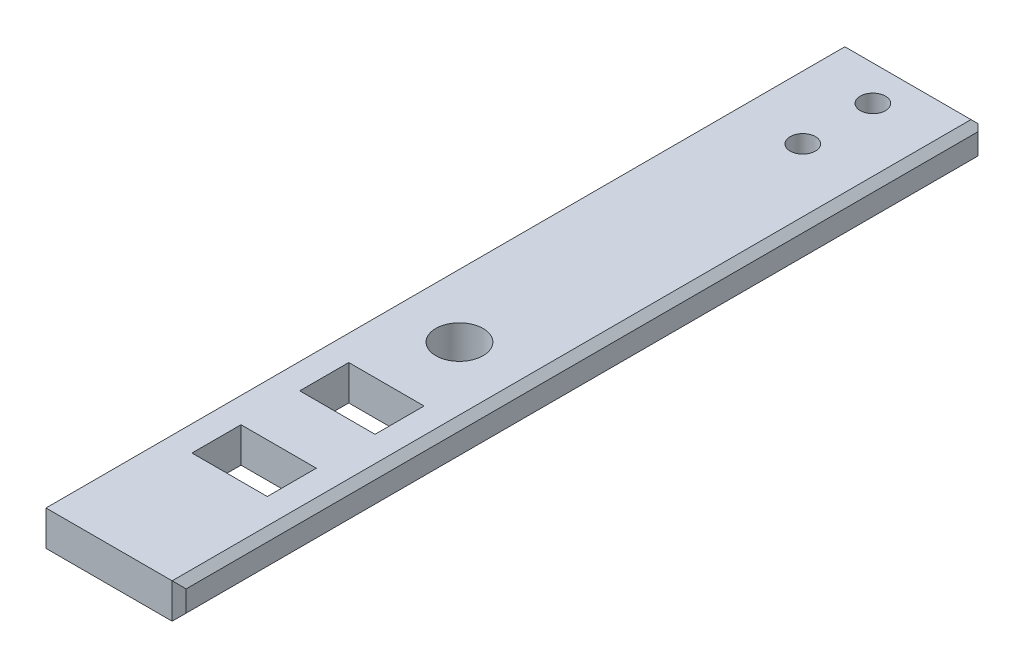
SolidWorks part; units mm, degrees
material "ABS"
ref_plane "Front Plane" through (0, 0, 0) normal (0, 0, 1) x (1, 0, 0)
ref_plane "Top Plane" through (0, 0, 0) normal (0, 1, 0) x (1, 0, 0)
ref_plane "Right Plane" through (0, 0, 0) normal (1, 0, 0) x (0, 0, -1)
sketch "Sketch1" plane through (0, 0, 0) normal (0, 1, 0) x (1, 0, 0)
  line L1 (0, 0) -> (20, 0)
  line L2 (0, 0) -> (0, 115)
  line L3 (0, 115) -> (20, 115)
  line L4 (20, 0) -> (20, 115)
  dimension "D1" = 20
  dimension "D2" = 115
extrude "Boss-Extrude1" add sketch "Sketch1" along normal blind 5
sketch "Sketch3" plane through (0, 0, 0) normal (0, -1, 0) x (1, 0, 0)
  line L1 (5, -25) -> (15, -25)
  line L2 (5, -25) -> (5, -33)
  line L3 (5, -33) -> (15, -33)
  line L4 (15, -25) -> (15, -33)
  line L5 (0, 0) -> (20, 0) construction
  line L6 (0, 0) -> (20, 0) construction
  point P4 (10, -25)
  point P5 (10, 0)
  dimension "D1" = 10
  dimension "D3" = 25
  dimension "D4" = 8
extrude "Boss-Extrude2" [suppressed] add sketch "Sketch3" along normal blind 12.5
sketch "Sketch13" [suppressed] plane through (10, 0, 0) normal (-1, 0, 0) x (0, 0, 1)
  line L4 (-25, 0) -> (-33, 0)
  line L5 (-33, 0) -> (-33, -12.5)
  line L6 (-33, -12.5) -> (-25, -12.5)
  line L7 (-25, -12.5) -> (-25, 0)
  line L8 (-25, 0) -> (-33, 0)
  line L9 (-33, 0) -> (-33, -12.5)
  line L10 (-33, -12.5) -> (-25, -12.5)
  line L11 (-25, -12.5) -> (-25, 0)
  dimension "D1" = 0
extrude "Cut-Extrude1" [suppressed] cut sketch "Sketch13" against normal mid plane 3.5
hole_wizard "M3 Clearance Hole5" [suppressed] positions "3DSketch5" profile "Sketch7" hole size "M3" standard "ANSI Metric"
sketch3d "3DSketch5" [suppressed]
  line L0 (5, -12.5, -25) -> (5, -12.5, -33) construction
  line L1 (5, -12.5, -33) -> (5, 0, -33) construction
  point P0 (5, -8.5, -29)
  dimension "D1" = 4
  dimension "D2" = 4
sketch "Sketch7" plane through (5, -8.5, -29) normal (0, 1, 0) x (0, 0, 1)
  line L0 (0, 0) -> (0, 15)
  line L1 (0, 15) -> (1.8, 15)
  line L2 (1.8, 15) -> (1.8, 0)
  line L5 (1.8, 0) -> (0, 0)
  line L11 (0, -6.35) -> (0, 107.95) construction
  dimension "Thru Hole Dia." = 3.6
  dimension "Thru Hole Depth" = 15
hole_wizard "E (0.29) Diameter Hole2" [suppressed] positions "3DSketch6" profile "Sketch8" hole size "E" standard "ANSI Inch"
sketch3d "3DSketch6"
  line L0 (20, 0, -75) -> (0, 0, -75) construction
  line L1 (20, 0, 0) -> (20, 0, -75) construction
  point P0 (10, 0, -40)
  dimension "D1" = 35
  dimension "D2" = 10
sketch "Sketch8" plane through (10, 0, -40) normal (1, 0, 0) x (0, 0, -1)
  line L0 (0, 0) -> (0, 5)
  line L1 (0, 5) -> (3.683, 5)
  line L2 (3.683, 5) -> (3.683, 0)
  line L5 (3.683, 0) -> (0, 0)
  line L11 (0, -6.35) -> (0, 107.95) construction
  dimension "Thru Hole Dia." = 7.366
  dimension "Thru Hole Depth" = 5
chamfer "Chamfer1" distance 1 angle 45 8 edges at (20, 2.5, -115) (20, 0, -57.5) (20, 5, -57.5) (0, 0, -57.5) (0, 2.5, -115) (0, 5, -57.5) (20, 2.5, 0) (0, 2.5, 0)
hole_wizard "E (0.29) Diameter Hole1" [suppressed] positions "3DSketch8" profile "Sketch10" hole size "E" standard "ANSI Inch"
sketch3d "3DSketch8"
  line L0 (19, 0, -75) -> (19, 0, 0) construction
  line L1 (1, 0, 0) -> (19, 0, 0) construction
  point P0 (10, 0, -7)
  dimension "D1" = 9
  dimension "D2" = 7
sketch "Sketch10" plane through (10, 0, -7) normal (1, 0, 0) x (0, 0, -1)
  line L0 (0, 0) -> (0, 5)
  line L1 (0, 5) -> (3.683, 5)
  line L2 (3.683, 5) -> (3.683, 0)
  line L5 (3.683, 0) -> (0, 0)
  line L11 (0, -6.35) -> (0, 107.95) construction
  dimension "Thru Hole Dia." = 7.366
  dimension "Thru Hole Depth" = 5
fillet "Fillet3" [suppressed] radius 1
chamfer "Chamfer2" distance 1 angle 45 2 edges at (10, 5, -115) (10, 0, -115)
sketch "Sketch15" [suppressed] plane through (0, 0, 0) normal (0, 1, 0) x (1, 0, 0)
  line L0 (10, 11) -> (10, 47) construction
  line L1 (1, 0) -> (19, 0) construction
  line L2 (8.25, 25) -> (8.25, 33) construction
  line L3 (8.25, 29) -> (10, 29) construction
  circle A0 centre (10, 11) radius 3.35
  circle A1 centre (10, 47) radius 3.35
  point P6 (10, 0)
  dimension "D2" = 6.7
  dimension "D1" = 18
extrude "Cut-Extrude2" [suppressed] cut sketch "Sketch15" against normal through all both and the other way through all
hole_wizard "M3 Clearance Hole6" positions "Sketch18" profile "Sketch17" hole size "M3" standard "ANSI Metric" end condition up to next
sketch "Sketch18" plane through (0, 0, 0) normal (0, -1, 0) x (-1, 0, 0)
  line L0 (-10, 109) -> (-10, 99)
  line L2 (-1, 114) -> (-19, 114) construction
  point P0 (-10, 109)
  point P2 (-10, 99)
  point P10 (-10, 114)
  dimension "D1" = 5
  dimension "D2" = 10
sketch "Sketch17" plane through (10, 0, -109) normal (1, 0, 0) x (0, 0, -1)
  line L0 (0, 0) -> (0, 5)
  line L1 (0, 5) -> (1.8, 5)
  line L2 (1.8, 5) -> (1.8, 0)
  line L5 (1.8, 0) -> (0, 0)
  line L11 (0, -6.35) -> (0, 107.95) construction
  dimension "Thru Hole Dia." = 3.6
  dimension "Thru Hole Depth" = 5
sketch "Sketch19" plane through (0, 0, 0) normal (0, 1, 0) x (1, 0, 0)
  line L1 (15.375, 17.2043) -> (4.625, 17.2043)
  line L2 (15.375, 17.2043) -> (15.375, 24.2043)
  line L3 (15.375, 24.2043) -> (4.625, 24.2043)
  line L4 (4.625, 17.2043) -> (4.625, 24.2043)
  line L5 (19, 0) -> (1, 0) construction
  line L6 (15, 17.2043) -> (5, 17.2043) construction
  point P8 (10, 0)
  point P9 (10, 17.2043)
  dimension "D1" = 10.75
  dimension "D2" = 7
extrude "Cut-Extrude3" cut sketch "Sketch19" along normal through all
ref_plane "Plane2" through (0, 0, -28.3918) normal (0, 0, 1) x (1, 0, 0)
mirror "Mirror1" about plane through (0, 0, -28.3918) normal (0, 0, 1) of "Cut-Extrude3"
sketch "Sketch20" plane through (0, 5, 0) normal (0, 1, 0) x (1, 0, 0)
  line L0 (1, 0) -> (19, 0) construction
  circle A0 centre (10, 50) radius 3.375
  point P4 (10, 0)
  dimension "D2" = 6.75
  dimension "D1" = 50
extrude "Cut-Extrude4" cut sketch "Sketch20" against normal blind 10
